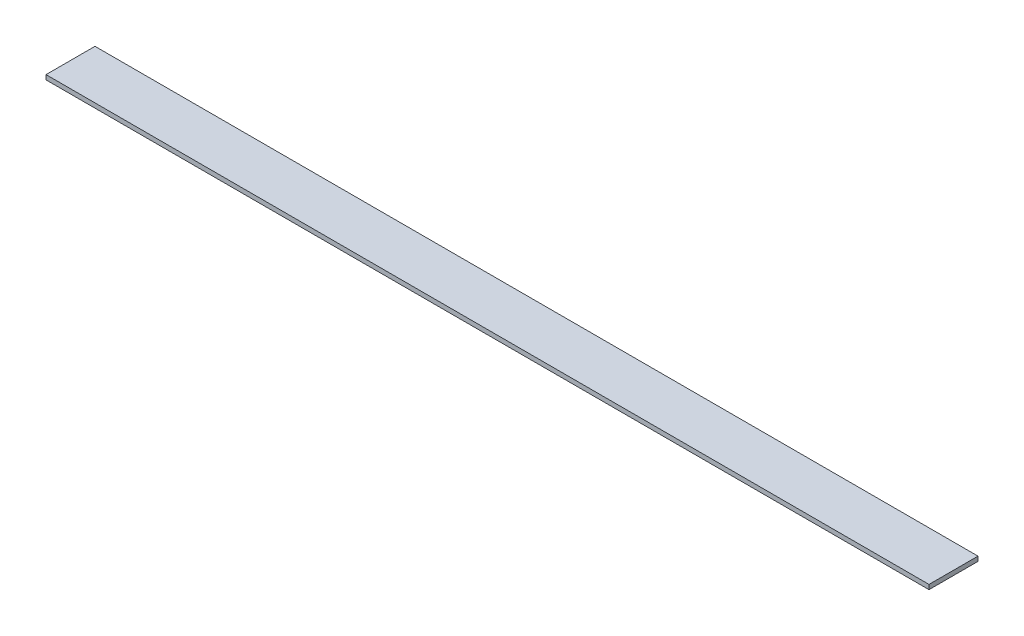
SolidWorks part; units mm, degrees
material "Acrylic (Medium-high impact)"
ref_plane "Front Plane" through (0, 0, 0) normal (0, 0, 1) x (1, 0, 0)
ref_plane "Top Plane" through (0, 0, 0) normal (0, 1, 0) x (1, 0, 0)
ref_plane "Right Plane" through (0, 0, 0) normal (1, 0, 0) x (0, 0, -1)
sketch "Sketch1" plane through (0, 0, 0) normal (0, 1, 0) x (1, 0, 0)
  line L1 (0, 0) -> (612.775, 0)
  line L2 (0, 0) -> (0, 34)
  line L3 (0, 34) -> (612.775, 34)
  line L4 (612.775, 0) -> (612.775, 34)
  dimension "D1" = 612.775
  dimension "D2" = 34
extrude "Boss-Extrude1" add sketch "Sketch1" along normal blind 3.175 contours L2 L3 L4 L1
